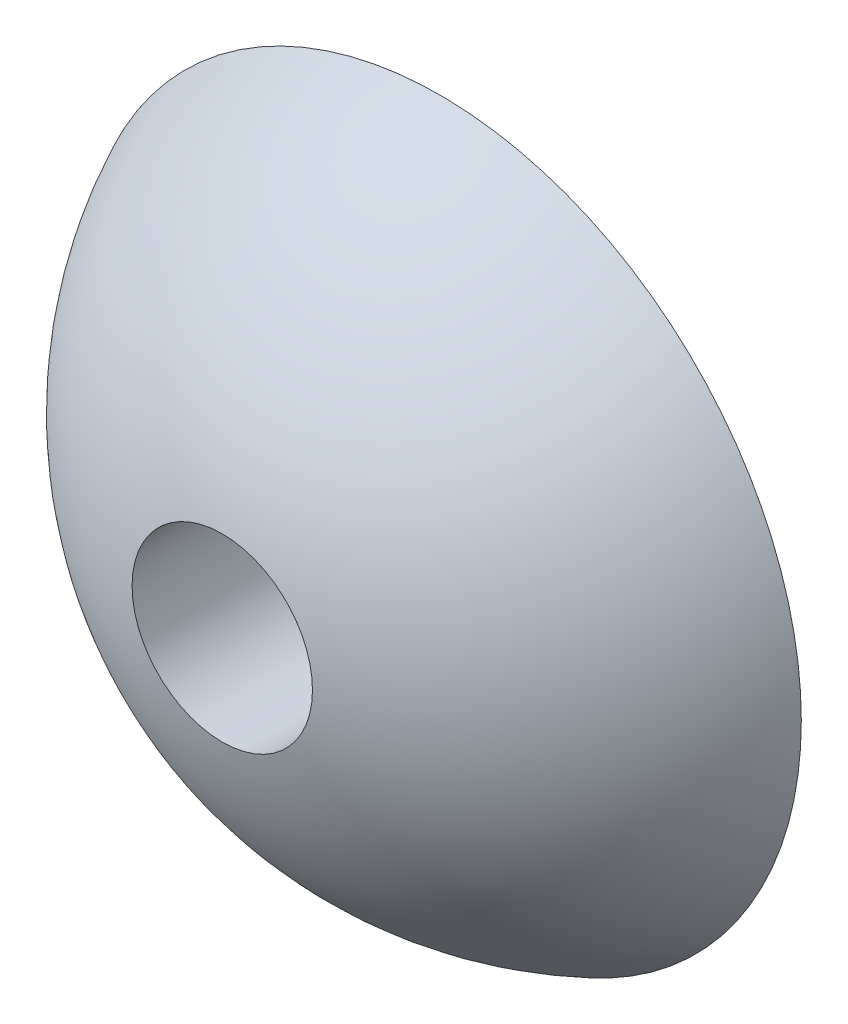
SolidWorks part; units mm, degrees
ref_plane "Front Plane" through (0, 0, 0) normal (0, 0, 1) x (1, 0, 0)
ref_plane "Top Plane" through (0, 0, 0) normal (0, 1, 0) x (1, 0, 0)
ref_plane "Right Plane" through (0, 0, 0) normal (1, 0, 0) x (0, 0, -1)
sketch "Sketch2" plane through (0, 0, 0) normal (0, 0, 1) x (1, 0, 0)
  line L0 (0, 0) -> (70, 0)
  arc A0 (0, 0) -> (70, 0) centre (35, 0) cw
  dimension "D1" = 70
revolve "Revolve1" add sketch "Sketch2" angle 360 about L0
ref_plane "Plane1" through (0, 0, 35) normal (0, 0, 1) x (1, 0, 0)
ref_plane "Plane2" through (0, 0, -5) normal (0, 0, 1) x (1, 0, 0)
sketch "Sketch6" plane through (0, 0, -5) normal (0, 0, 1) x (1, 0, 0)
  line L0 (17.5, -7) -> (52.5, -7) construction
  circle A0 centre (35, -7) radius 22.5
  circle A1 centre (17.5, -7) radius 1
  circle A2 centre (52.5, -7) radius 1
  dimension "D1" = 45
extrude "Cut-Extrude8" cut sketch "Sketch6" along normal blind 20
sketch "Sketch7" plane through (0, 0, 35) normal (0, 0, 1) x (1, 0, 0)
  line L0 (0, 0) -> (70, 0) construction
  circle A0 centre (35, 0) radius 35 construction
  circle A1 centre (35, 0) radius 7.9
  dimension "D1" = 15.8
extrude "Cut-Extrude9" cut sketch "Sketch7" against normal blind 20
ref_plane "Plane3" through (0, 0, -35) normal (0, 0, 1) x (1, 0, 0)
sketch "Sketch9" plane through (0, 0, -35) normal (0, 0, 1) x (1, 0, 0)
  line L1 (-1.9981, 37.2014) -> (72.9129, 37.2014)
  line L2 (-1.9981, 37.2014) -> (-1.9981, -37.4047)
  line L3 (-1.9981, -37.4047) -> (72.9129, -37.4047)
  line L4 (72.9129, 37.2014) -> (72.9129, -37.4047)
extrude "Cut-Extrude11" cut sketch "Sketch9" along normal blind 50
